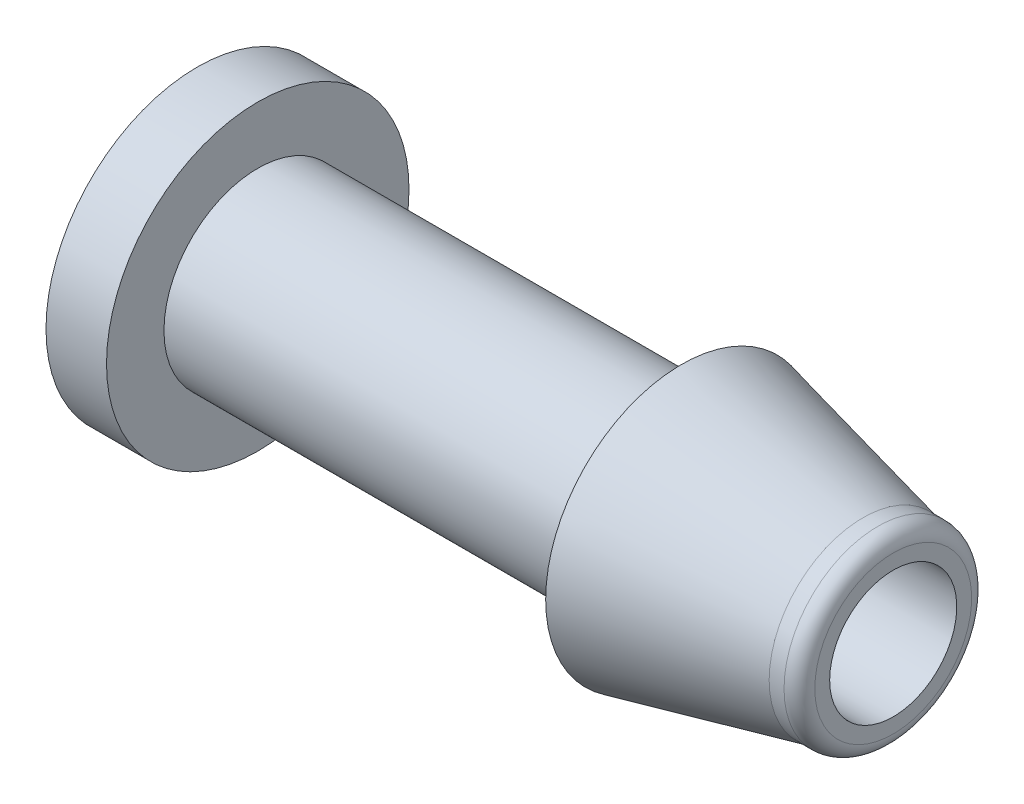
SolidWorks part; units mm, degrees
ref_plane "Front Plane" through (0, 0, 0) normal (0, 0, 1) x (1, 0, 0)
ref_plane "Top Plane" through (0, 0, 0) normal (0, 1, 0) x (1, 0, 0)
ref_plane "Right Plane" through (0, 0, 0) normal (1, 0, 0) x (0, 0, -1)
sketch "Sketch1" plane through (0, 0, 0) normal (0, 0, 1) x (1, 0, 0)
  line L0 (0, 0) -> (8.3844, 0) construction
  line L1 (0, 2.1) -> (8.3844, 2.1)
  line L2 (0, 3.1) -> (14, 3.1)
  line L3 (0, 3.1) -> (0, 2.1)
  line L4 (14, 3.1) -> (14, 4.4852)
  line L6 (21, 2.592) -> (21, 2.1)
  line L7 (21, 2.1) -> (8.3844, 2.1)
  line L8 (14, 4.4852) -> (20, 3.1)
  line L9 (20, 3.1) -> (20.492, 3.1)
  line L10 (0, 0) -> (0, 3.1) construction
  arc A0 (21, 2.592) -> (20.492, 3.1) centre (20.492, 2.592) ccw
  point P7 (14, 3.7926)
  point P14 (21, 3.1)
  point P15 (0, 0)
  dimension "D6" = 0.508
  dimension "D1" = 3.1
  dimension "D2" = 1
  dimension "D3" = 1
  dimension "D4" = 6
  dimension "D5" = 13
  dimension "D7" = 21
revolve "Revolve2" add sketch "Sketch1" angle 360 about L0
sketch "Sketch2" plane through (0, 0, 0) normal (-1, 0, 0) x (0, 0, 1)
  circle A0 centre (0, 0) radius 2.1
  circle A1 centre (0, 0) radius 4.9979
extrude "Boss-Extrude1" add sketch "Sketch2" along normal blind 2
